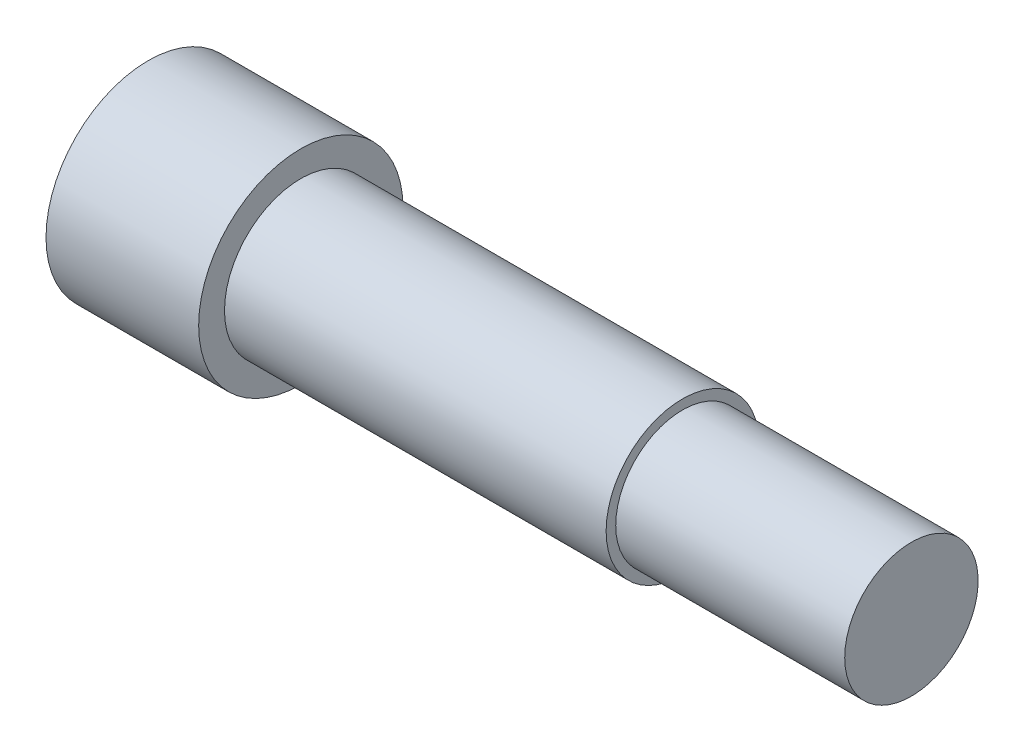
SolidWorks part; units mm, degrees
ref_plane "Front Plane" through (0, 0, 0) normal (0, 0, 1) x (1, 0, 0)
ref_plane "Top Plane" through (0, 0, 0) normal (0, 1, 0) x (1, 0, 0)
ref_plane "Right Plane" through (0, 0, 0) normal (1, 0, 0) x (0, 0, -1)
sketch "Sketch1" plane through (0, 0, 0) normal (0, 0, 1) x (1, 0, 0)
  line L0 (0, 0) -> (63.5, 0)
  line L1 (63.5, 0) -> (63.5, 5.5499)
  line L2 (63.5, 5.5499) -> (44.45, 5.5499)
  line L3 (12.7, 6.35) -> (12.7, 8.5)
  line L4 (12.7, 8.5) -> (0, 8.5)
  line L5 (0, 8.5) -> (0, 0)
  line L6 (12.7, 6.35) -> (44.45, 6.35)
  line L7 (44.45, 6.35) -> (44.45, 5.5499)
  dimension "D2" = 5.5499
  dimension "D4" = 12.7
  dimension "D3" = 8.5
  dimension "D1" = 31.75
  dimension "D5" = 19.05
  dimension "D6" = 6.35
revolve "Revolve1" add sketch "Sketch1" angle 360 about L0
cosmetic thread "Cosmetic Thread1" parameters "D2"=9.6012
equation "\"after_laby_len\"= 1.25"
equation "\"D1@Sketch1\"=\"after_laby_len\""
equation "\"Cavity_Depth\" = 0.031in"
equation "\"Cavity_Width\" = 0.031in"
equation "\"Tooth_Width\" = .01in"
equation "\"Shaft_Seal_OD\"= 17mm'diameter at seal area"
equation "\"Shaft_clearance\"= .002in"
equation "\"O-Ring_ID\"= .801in"
equation "\"O-Ring_CS\"= .070in"
equation "\"Shaft_OD\"= .5in"
equation "\"D3@Sketch1\"=\"Shaft_Seal_OD\"/2"
equation "\"D6@Sketch1\"=\"Shaft_OD\"/2"
